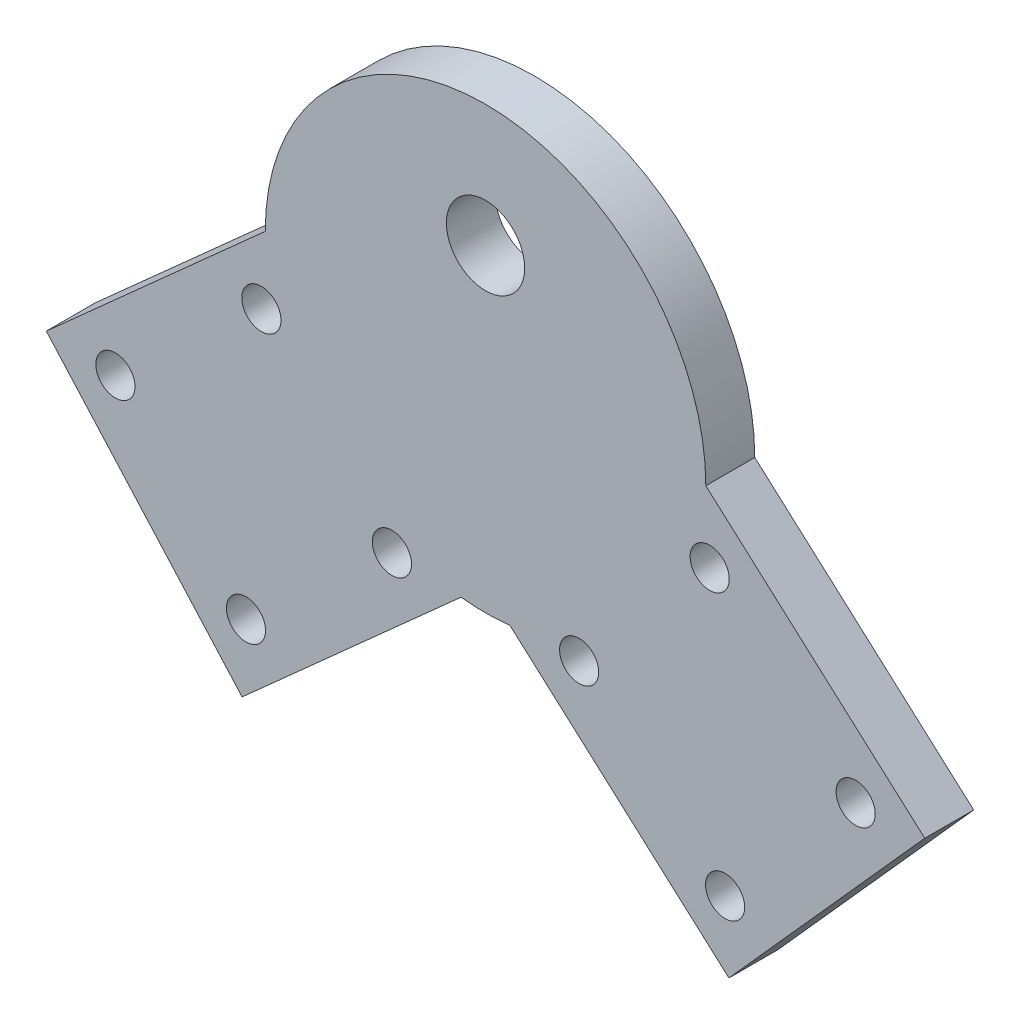
SolidWorks part; units mm, degrees
ref_plane "Front Plane" through (0, 0, 0) normal (0, 0, 1) x (1, 0, 0)
ref_plane "Top Plane" through (0, 0, 0) normal (0, 1, 0) x (1, 0, 0)
ref_plane "Right Plane" through (0, 0, 0) normal (1, 0, 0) x (0, 0, -1)
sketch "Sketch2" plane through (0, 0, 0) normal (0, 0, 1) x (1, 0, 0)
  line L0 (-22.5, 0) -> (-2.5, -22.3607)
  line L1 (-22.5, 0) -> (-44.8607, -20)
  line L2 (-2.5, -22.3607) -> (-24.8607, -42.3607)
  line L3 (-44.8607, -20) -> (-24.8607, -42.3607)
  line L4 (2.5, -22.3607) -> (22.5, 0)
  line L5 (2.5, -22.3607) -> (24.8607, -42.3607)
  line L6 (22.5, 0) -> (44.8607, -20)
  line L7 (24.8607, -42.3607) -> (44.8607, -20)
  line L8 (-22.5, 0) -> (0, 0)
  line L9 (0, 0) -> (-2.5, -22.3607)
  line L10 (2.5, -22.3607) -> (0, 0)
  line L11 (22.5, 0) -> (0, 0)
  circle A0 centre (0, 0) radius 22.5
  dimension "D5" = 45
  dimension "D1" = 30
  dimension "D2" = 30
  dimension "D3" = 30
  dimension "D4" = 30
extrude "Boss-Extrude1" add sketch "Sketch2" along normal blind 5 contours L0 L1 L3 L2 | L4 L5 L7 L6 | A0
sketch "Sketch3" plane through (0, 0, 0) normal (0, 0, -1) x (-1, 0, 0)
  line L0 (2.5, -22.3607) -> (24.8607, -42.3607) construction
  line L1 (44.8607, -20) -> (24.8607, -42.3607) construction
  line L2 (-22.5, 0) -> (-44.8607, -20) construction
  line L3 (-24.8607, -42.3607) -> (-44.8607, -20) construction
  line L4 (-22.5, 0) -> (-2.5, -22.3607)
  line L5 (-2.5, -22.3607) -> (-24.8607, -42.3607) construction
  line L6 (-37.8006, -20.3934) -> (-22.8934, -7.0601)
  line L7 (-22.8934, -7.0601) -> (-9.5601, -21.9672)
  line L8 (-9.5601, -21.9672) -> (-24.4672, -35.3006)
  line L9 (-37.8006, -20.3934) -> (-24.4672, -35.3006)
  line L10 (22.5, 0) -> (44.8607, -20) construction
  line L11 (24.4672, -35.3006) -> (37.8006, -20.3934)
  line L12 (37.8006, -20.3934) -> (22.8934, -7.0601)
  line L13 (22.8934, -7.0601) -> (9.5601, -21.9672)
  line L14 (9.5601, -21.9672) -> (24.4672, -35.3006)
  circle A0 centre (-37.8006, -20.3934) radius 2
  circle A1 centre (-22.8934, -7.0601) radius 2
  circle A2 centre (-9.5601, -21.9672) radius 2
  circle A3 centre (-24.4672, -35.3006) radius 2
  circle A4 centre (24.4672, -35.3006) radius 2
  circle A5 centre (37.8006, -20.3934) radius 2
  circle A6 centre (9.5601, -21.9672) radius 2
  circle A7 centre (22.8934, -7.0601) radius 2
  dimension "D3" = 4
  dimension "D7" = 4
  dimension "D8" = 4
  dimension "D9" = 4
  dimension "D12" = 4
  dimension "D15" = 4
  dimension "D16" = 4
  dimension "D17" = 4
  dimension "D1" = 5
  dimension "D2" = 5
  dimension "D4" = 30
  dimension "D5" = 5
  dimension "D6" = 5
  dimension "D10" = 5
  dimension "D11" = 5
  dimension "D13" = 5
  dimension "D14" = 5
extrude "Cut-Extrude1" cut sketch "Sketch3" against normal blind 5 from surface at 0 contours A1 | A0 | A3 | A2 | A6 | A7 | A5 | A4 starting at face at (0, -18.3853, 0)
sketch "Sketch4" plane through (0, 0, 0) normal (0, 0, -1) x (-1, 0, 0)
  line L0 (-22.5, 0) -> (22.5, 0) construction
  line L1 (0, 0) -> (0, 22.5) construction
  arc A0 (22.5, 0) -> (-22.5, 0) centre (0, 0) ccw construction
  circle A1 centre (0, 10) radius 4
  dimension "D1" = 8
  dimension "D2" = 10
extrude "Cut-Extrude2" cut sketch "Sketch4" against normal blind 10
